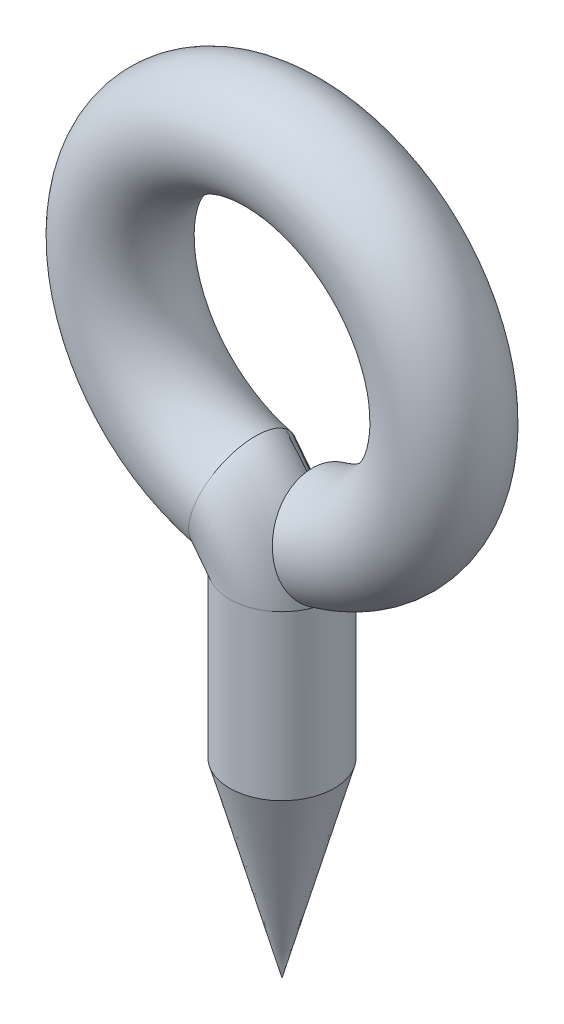
SolidWorks part; units mm, degrees
ref_plane "Plan de face" through (0, 0, 0) normal (0, 0, 1) x (1, 0, 0)
ref_plane "Plan de dessus" through (0, 0, 0) normal (0, 1, 0) x (1, 0, 0)
ref_plane "Plan de droite" through (0, 0, 0) normal (1, 0, 0) x (0, 0, -1)
sketch "Esquisse1" plane through (0, 0, 0) normal (0, 0, 1) x (1, 0, 0)
  line L0 (0, -15.049) -> (0, 44.91) construction
  line L1 (0, 7.4365) -> (0, 4)
  line L2 (-3.5923, 4) -> (5.3111, 4) construction
  line L3 (9.6667, 15.2) -> (-7.7557, 15.2) construction
  line L5 (-3.1439, 11.8) -> (3.8379, 11.8) construction
  line L6 (0, 11.8) -> (1.8366, 5.3949) construction
  arc A0 (0.9372, 8.5317) -> (-0.8311, 8.5031) centre (0, 11.8) ccw
  arc A1 (0, 7.4365) -> (-0.8311, 8.5031) centre (-1.1, 7.4365) ccw
  point P18 (0, 8.4)
  dimension "D3" = 1.1
  dimension "D1" = 3.4
  dimension "D2" = 74
ref_plane "Plan1" through (0, 4, 0) normal (0, 1, 0) x (-1, 0, 0)
sketch "Esquisse6" plane through (0, 4, 0) normal (0, 1, 0) x (-1, 0, 0)
  circle A0 centre (0, 0) radius 1.1
sweep "Balayage7" add profiles "Esquisse6" path "Esquisse1"
sketch "Esquisse7" plane through (0, 0, 0) normal (0, 0, 1) x (1, 0, 0)
  line L0 (0, -0.755) -> (0, 5.6638) construction
  line L1 (-1.1, 1.9597) -> (-1.1, 5.1381) construction
  line L2 (3.9805, 4) -> (-7.1464, 4) construction
  line L3 (0, 4) -> (-1.1, 4)
  line L4 (-1.1, 4) -> (0, 0)
  line L5 (0, 4) -> (0, 0)
revolve "Révolution2" add sketch "Esquisse7" angle 360 about L5
